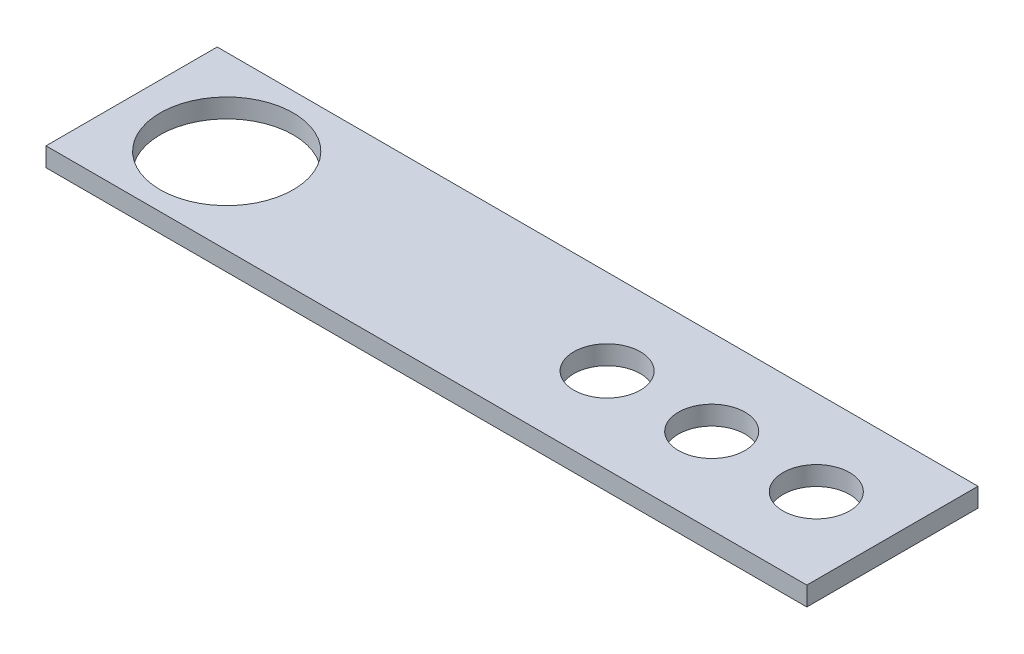
SolidWorks part; units mm, degrees
ref_plane "Front Plane" through (0, 0, 0) normal (0, 0, 1) x (1, 0, 0)
ref_plane "Top Plane" through (0, 0, 0) normal (0, 1, 0) x (1, 0, 0)
ref_plane "Right Plane" through (0, 0, 0) normal (1, 0, 0) x (0, 0, -1)
sketch "Sketch2" plane through (0, 0, 0) normal (0, 1, 0) x (1, 0, 0)
  line L1 (-20, -4.5) -> (20, -4.5)
  line L2 (-20, -4.5) -> (-20, 4.5)
  line L3 (-20, 4.5) -> (20, 4.5)
  line L4 (20, -4.5) -> (20, 4.5)
  line L5 (0, 4.5) -> (0, -4.5) construction
  line L6 (-20, 0) -> (20, 0) construction
  point P0 (0, 0)
  dimension "D1" = 9
  dimension "D2" = 40
extrude "Boss-Extrude1" add sketch "Sketch2" along normal blind 1
sketch "Sketch3" plane through (0, 1, 0) normal (0, 1, 0) x (1, 0, 0)
  line L0 (-20, 4.5) -> (-20, -4.5) construction
  line L1 (-1, 2) -> (-12.7729, 2.7)
  line L2 (-12.7729, 2.7) -> (-12.7729, -2.7)
  line L3 (-12.7729, -2.7) -> (-1, -2)
  line L4 (-20, 0) -> (20, 0) construction
  line L5 (20, -4.5) -> (20, 4.5) construction
  circle A0 centre (-15, 0) radius 3.5
  circle A1 centre (-1, 0) radius 2
  point P9 (0, 0)
  point P11 (0, 0)
  dimension "D1" = 7
  dimension "D2" = 5
  dimension "D3" = 4
  dimension "D4" = 14
  dimension "D5" = 5.4
extrude "Cut-Extrude1" cut sketch "Sketch3" against normal blind 3 contours A0
sketch "Sketch4" plane through (0, 1, 0) normal (0, 1, 0) x (1, 0, 0)
  line L0 (-20, 0) -> (20, 0) construction
  line L1 (-20, 4.5) -> (-20, -4.5) construction
  line L2 (20, -4.5) -> (20, 4.5) construction
  circle A0 centre (5, 0) radius 1.75
  circle A1 centre (-15, 0) radius 3.5 construction
  dimension "D1" = 3.5
  dimension "D2" = 20
extrude "Cut-Extrude2" cut sketch "Sketch4" against normal blind 3
pattern_linear "LPattern1" count 3 spacing 5.5 along (1, 0, 0) of "Cut-Extrude2"
